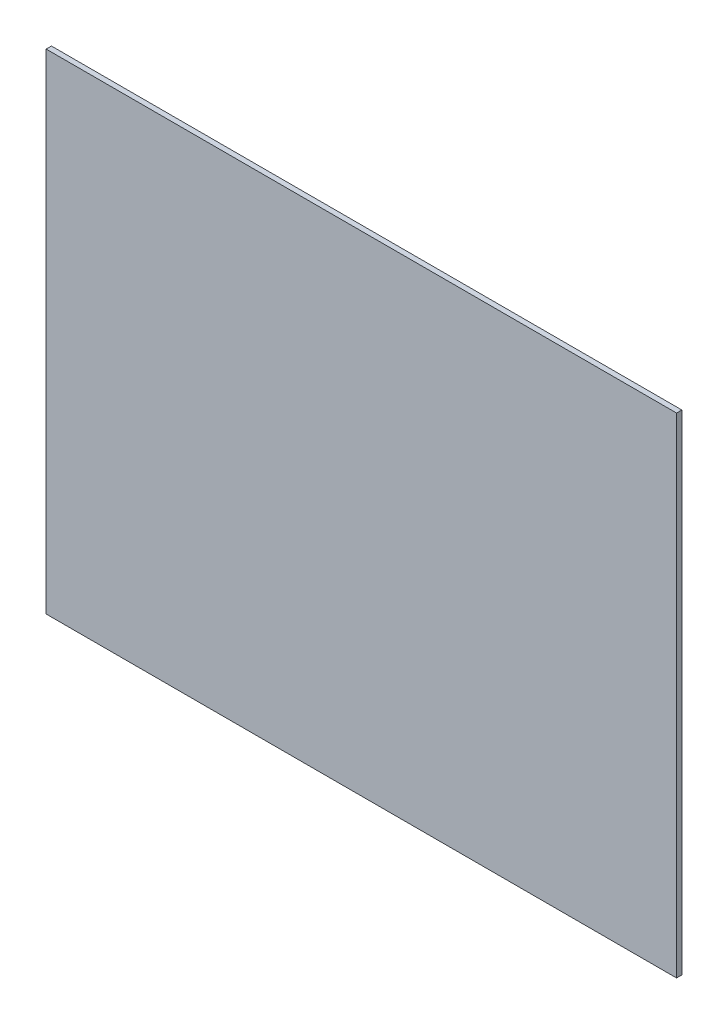
SolidWorks part; units mm, degrees
material "Acrylic (Medium-high impact)"
ref_plane "Front Plane" through (0, 0, 0) normal (0, 0, 1) x (1, 0, 0)
ref_plane "Top Plane" through (0, 0, 0) normal (0, 1, 0) x (1, 0, 0)
ref_plane "Right Plane" through (0, 0, 0) normal (1, 0, 0) x (0, 0, -1)
sketch "Sketch1" plane through (0, 0, 0) normal (0, 0, 1) x (1, 0, 0)
  line L1 (-268, -208) -> (268, -208)
  line L2 (-268, -208) -> (-268, 208)
  line L3 (-268, 208) -> (268, 208)
  line L4 (268, -208) -> (268, 208)
  line L5 (-268, -208) -> (268, 208) construction
  line L6 (-268, 208) -> (268, -208) construction
  point P0 (0, 0)
  dimension "D1" = 536
  dimension "D2" = 416
extrude "Boss-Extrude1" add sketch "Sketch1" along normal mid plane 4.4958
